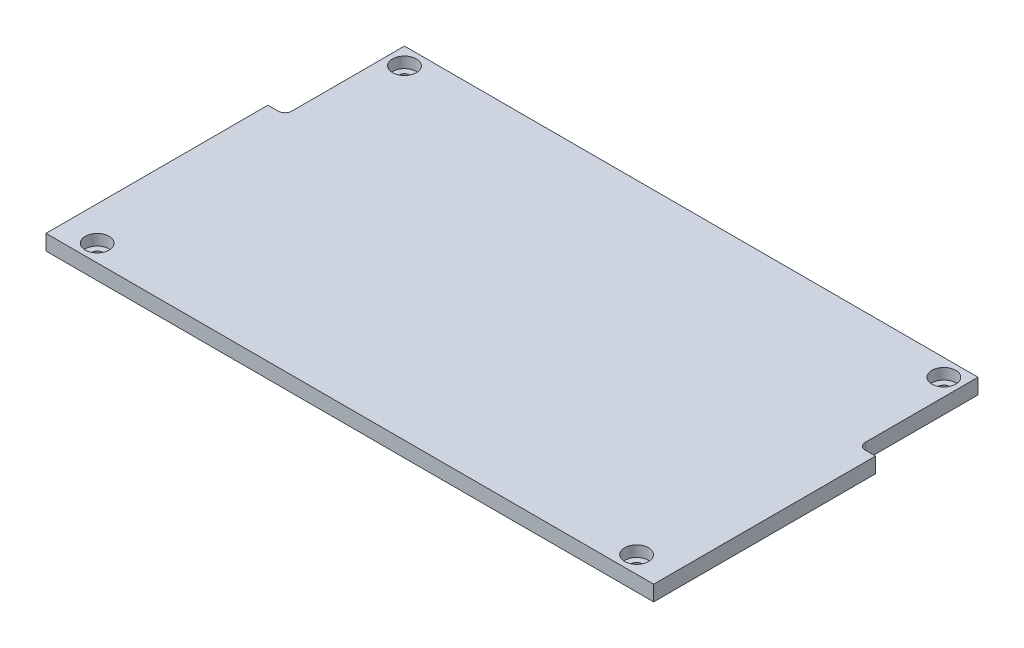
SolidWorks part; units mm, degrees
ref_plane "Ebene vorne" through (0, 0, 0) normal (0, 0, 1) x (1, 0, 0)
ref_plane "Ebene oben" through (0, 0, 0) normal (0, 1, 0) x (1, 0, 0)
ref_plane "Ebene rechts" through (0, 0, 0) normal (1, 0, 0) x (0, 0, -1)
sketch "Skizze1" plane through (0, 0, 0) normal (0, 1, 0) x (1, 0, 0)
  line L1 (0, 0) -> (-89, 0)
  line L2 (0, 0) -> (0, 50)
  line L3 (0, 50) -> (-89, 50)
  line L4 (-89, 0) -> (-89, 50)
  dimension "D1" = 89
  dimension "D2" = 50
extrude "Aufsatz-Linear austragen1" add sketch "Skizze1" along normal blind 4.5
sketch "Skizze3" plane through (0, 4.5, 0) normal (0, 1, 0) x (1, 0, 0)
  line L1 (0, 0) -> (0, 50) construction
  line L2 (-19, 3) -> (-3, 3)
  line L3 (-19, 3) -> (-19, 15)
  line L4 (-19, 15) -> (-3, 15)
  line L5 (-3, 3) -> (-3, 15)
  line L6 (-19, 3) -> (-3, 15) construction
  line L7 (-19, 15) -> (-3, 3) construction
  line L8 (-89, 0) -> (0, 0) construction
  point P0 (-11, 9)
  dimension "D1" = 3
  dimension "D3" = 12
  dimension "D2" = 3
  dimension "D4" = 16
extrude "Schnitt-Linear austragen2" cut sketch "Skizze3" against normal through all
fillet "Verrundung1" radius 2 4 edges at (-19, 2.25, -3) (-3, 2.25, -3) (-3, 2.25, -15) (-19, 2.25, -15)
pattern_linear "Lineares Muster1" count 3 spacing 16 along (0, 0, -1) count 4 spacing 20 along (-1, 0, 0) of "Schnitt-Linear austragen2", "Verrundung1"
sketch "Skizze2" plane through (0, 4.5, 0) normal (0, 1, 0) x (1, 0, 0)
  line L0 (0, 0) -> (0, 50) construction
  line L1 (-89, 0) -> (0, 0) construction
  circle A0 centre (-79, 45) radius 5
  dimension "D1" = 10
  dimension "D2" = 79
  dimension "D3" = 45
extrude "Aufsatz-Linear austragen2" add sketch "Skizze2" against normal up to surface (4.5 mm away) up to face at (-11, 0, -25)
hole_wizard "Stirnsenkung für M3 Flachkopfschraube mit Schlitz1" positions "Skizze4" profile "Skizze5" counterbore size "M3" standard "DIN" end condition through all
sketch "Skizze4" plane through (0, 4.5, 0) normal (0, 1, 0) x (1, 0, 0)
  line L0 (0, 50) -> (-89, 50) construction
  point P0 (-79, 45)
  dimension "D1" = 10
  dimension "D2" = 5
sketch "Skizze5" plane through (-79, 4.5, -45) normal (1, 0, 0) x (0, 0, 1)
  line L0 (0, 0) -> (0, 4.5)
  line L1 (0, 4.5) -> (1.7, 4.5)
  line L3 (1.7, 4.5) -> (1.7, 3.2)
  line L4 (1.7, 3.2) -> (3.5, 3.2)
  line L5 (3.5, 3.2) -> (3.5, 0)
  line L7 (3.5, 0) -> (0, 0)
  line L11 (0, -6.35) -> (0, 107.95) construction
  dimension "Bohrerdurchmesser" = 3.4
  dimension "Bohrungstiefe" = 4.5
  dimension "Senkdurchmesser2" = 7
  dimension "Senktiefe2" = 3.2
fillet "Verrundung3" radius 3 2 edges at (-79, 2.25, -40) (-74.4174, 2.25, -47)
sketch "Skizze6" plane through (0, 0, 0) normal (0, -1, 0) x (1, 0, 0)
  line L0 (-79, -29) -> (-79, -21) construction
  line L1 (0, 0) -> (-79, 0)
  line L2 (0, 0) -> (0, -47)
  line L3 (0, -47) -> (-71.0627, -47)
  line L4 (-79, 0) -> (-79, -37)
  line L5 (-71.0627, -37) -> (-79, -37)
  line L6 (-71.0627, -37) -> (-71.0627, -47)
  line L11 (-45, -47) -> (-57, -47) construction
  line L12 (-65, -47) -> (-71.0627, -47) construction
extrude "Schnitt-Linear austragen3" cut sketch "Skizze6" against normal blind 1.5
sketch "Skizze7" plane through (0, 1.5, 0) normal (0, -1, 0) x (1, 0, 0)
  line L0 (-79, 0) -> (0, 0)
  line L1 (0, 0) -> (0, -47)
  line L6 (0, -50) -> (0, -47)
  line L7 (0, -47) -> (-71.0627, -47)
  line L8 (-79, -37.5838) -> (-79, 0)
  line L9 (-79, 0) -> (-89, 0)
  line L10 (-89, 0) -> (-89, -50)
  line L11 (-89, -50) -> (0, -50)
  line L13 (0, -47) -> (-71.0627, -47)
  line L14 (-79, -37.5838) -> (-79, 0)
  arc A3 (-74.0392, -44.375) -> (-71.0627, -47) centre (-71.0627, -44) ccw
  arc A4 (-74.0392, -44.375) -> (-77.125, -40.3649) centre (-79, -45) ccw
  arc A5 (-79, -37.5838) -> (-77.125, -40.3649) centre (-76, -37.5838) ccw
  arc A6 (-74.0392, -44.375) -> (-71.0627, -47) centre (-71.0627, -44) ccw
  arc A7 (-74.0392, -44.375) -> (-77.125, -40.3649) centre (-79, -45) ccw
  arc A8 (-79, -37.5838) -> (-77.125, -40.3649) centre (-76, -37.5838) ccw
  dimension "D1" = 0
extrude "Aufsatz-Linear austragen3" add sketch "Skizze7" against normal up to surface (3 mm away) up to face at (-79, 4.5, -41.5)
mirror "Spiegeln1" about plane through (0, 4.5, 0) normal (0, 0, -1) of bodies 124 115
sketch "Skizze8" plane through (0, 0, 0) normal (0, -1, 0) x (1, 0, 0)
  line L5 (0, -50) -> (-89, -50) construction
  line L7 (-89, -50) -> (-89, 50) construction
  line L9 (-94, -50) -> (-84, -50)
  line L10 (-94, -50) -> (-94, -15)
  line L11 (-94, -15) -> (-84, -15)
  line L12 (-84, -50) -> (-84, -15)
  line L13 (-94, -50) -> (-84, -15) construction
  line L14 (-94, -15) -> (-84, -50) construction
  point P2 (-84, -54.1289)
  point P9 (-89, -32.5)
  dimension "D1" = 35
  dimension "D4" = 5
extrude "Schnitt-Linear austragen4" cut sketch "Skizze8" against normal through all
fillet "Verrundung4" radius 2 1 edges at (-84, 2.25, -15)
mirror "Spiegeln2" about plane through (0, 4.5, 0) normal (-1, 0, 0) of bodies 125 116
